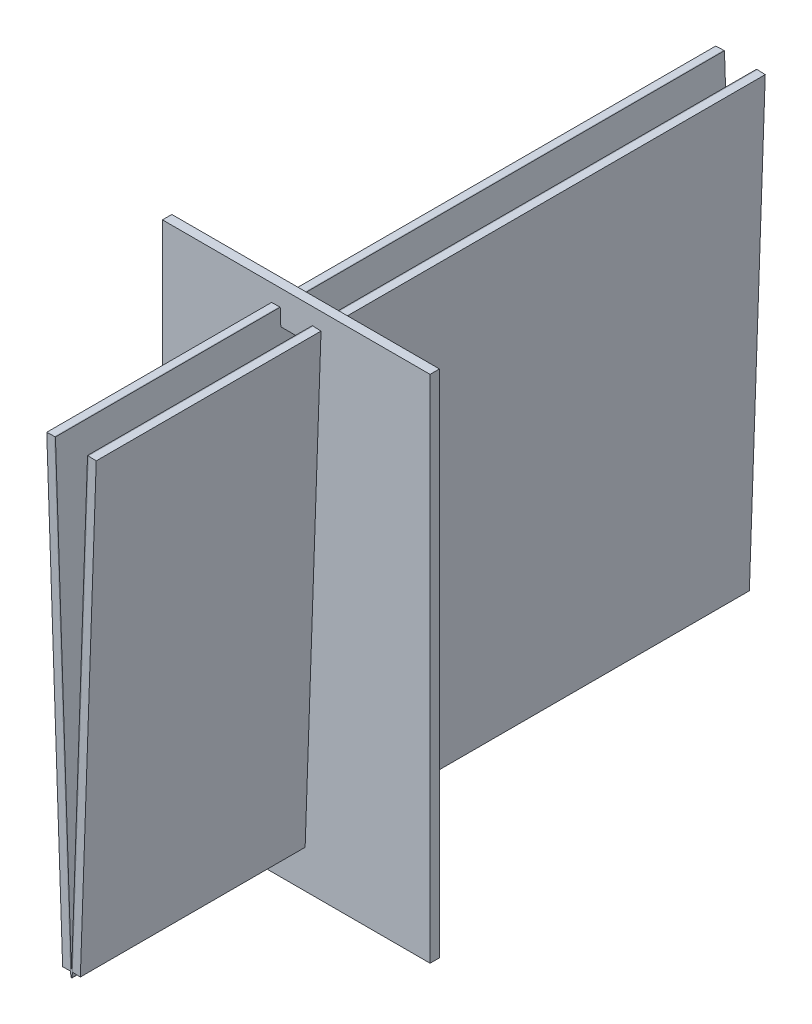
SolidWorks part; units mm, degrees
ref_plane "Front" through (0, 0, 0) normal (0, 0, 1) x (1, 0, 0)
ref_plane "Top" through (0, 0, 0) normal (0, 1, 0) x (1, 0, 0)
ref_plane "Right" through (0, 0, 0) normal (1, 0, 0) x (0, 0, -1)
ref_plane "Plane1" through (0, 0, 30) normal (0, 0, 1) x (1, 0, 0)
sketch "Sketch2" plane through (0, 0, 0) normal (0, 0, 1) x (1, 0, 0)
  line L0 (-0.25, 0) -> (-5, 136.0222)
  line L1 (-0.25, 0) -> (-2.6485, -0.0838)
  line L2 (-5, 136.0222) -> (-7.3985, 135.9384)
  line L3 (-2.6485, -0.0838) -> (-7.3985, 135.9384)
  line L4 (0.25, 0) -> (5, 136.0222)
  line L5 (0.25, 0) -> (2.6485, -0.0838)
  line L6 (5, 136.0222) -> (7.3985, 135.9384)
  line L7 (2.6485, -0.0838) -> (7.3985, 135.9384)
  line L8 (-0.25, 0) -> (0, 0) construction
  line L9 (0, 0) -> (0.25, 0) construction
  line L10 (-5, 136.0222) -> (5, 136.0222) construction
  point P0 (0, 136.0222)
  dimension "D1" = 2.4
  dimension "D2" = 4
  dimension "D3" = 0.5
  dimension "D4" = 10
extrude "Boss-Extrude1" add sketch "Sketch2" along normal mid plane 200
sketch "Sketch4" plane through (0, 0, 0) normal (0, 0, 1) x (1, 0, 0)
  line L0 (-5, 136.0222) -> (-0.1999, -1.4353)
  line L1 (5, 136.0222) -> (0.1999, -1.4353)
  line L2 (5, 136.0222) -> (0.25, 0) construction
  line L3 (-0.25, 0) -> (-5, 136.0222) construction
  line L4 (4.8001, 136.0292) -> (0, -1.4283)
  line L5 (-4.8001, 136.0292) -> (0, -1.4283)
  line L6 (-5, 136.0222) -> (-4.8001, 136.0292)
  line L7 (4.8001, 136.0292) -> (5, 136.0222)
  arc A0 (0.1999, -1.4353) -> (-0.1999, -1.4353) centre (0, -1.4283) cw
  arc A1 (0, -1.4283) -> (0, -1.4283) centre (0, -1.4283) cw
  dimension "D1" = 0.2
  dimension "D2" = 0.2
extrude "Boss-Extrude2" add sketch "Sketch4" along normal up to surface and the other way up to surface separate body up to face at (-3.8243, 67.9692, 100) other way up to face at (-3.8243, 67.9692, -100)
sketch "Sketch5" plane through (0, 0, 30) normal (0, 0, 1) x (1, 0, 0)
  line L0 (40, -11.4351) -> (-40, -11.4351)
  line L1 (-40, -11.4351) -> (-40, 141.0292)
  line L2 (-4.8001, 136.0292) -> (-4.6255, 131.0292)
  line L3 (-7.3985, 135.9384) -> (-2.9008, 7.1399)
  line L4 (-2.9008, 7.1399) -> (2.9008, 7.1399)
  line L5 (2.9008, 7.1399) -> (7.3985, 135.9384)
  line L7 (40, 141.0292) -> (40, -11.4351)
  line L8 (-7.3985, 135.9384) -> (-2.6485, -0.0838) construction
  line L9 (2.6485, -0.0838) -> (7.3985, 135.9384) construction
  line L11 (-4.8001, 136.0292) -> (0, -1.4283) construction
  line L12 (4.8001, 136.0292) -> (7.3985, 135.9384)
  line L13 (-4.6255, 131.0292) -> (4.6255, 131.0292)
  line L14 (-4.8001, 136.0292) -> (-7.3985, 135.9384)
  line L16 (0, -1.4283) -> (4.8001, 136.0292) construction
  line L17 (7.3985, 135.9384) -> (5, 136.0222) construction
  line L18 (-5, 136.0222) -> (-7.3985, 135.9384) construction
  line L19 (-40, 141.0292) -> (40, 141.0292)
  line L20 (4.6255, 131.0292) -> (4.8001, 136.0292)
  line L21 (-3.25, 17.1399) -> (3.25, 17.1399) construction
  point P25 (0, 141.0292)
  dimension "D1" = 28.575
  dimension "D2" = 10
  dimension "D3" = 5
  dimension "D4" = 80
  dimension "D5" = 5
  dimension "D6" = 6.5
extrude "Boss-Extrude3" add sketch "Sketch5" along normal blind 2.8 separate body
sketch "Sketch6" plane through (0, 0, 32.8) normal (0, 0, 1) x (1, 0, 0)
  line L0 (-3, 9.9808) -> (3, 9.9808)
  line L1 (-7.3985, 135.9384) -> (-2.9008, 7.1399) construction
  line L2 (2.9008, 7.1399) -> (7.3985, 135.9384) construction
  dimension "D1" = 6
